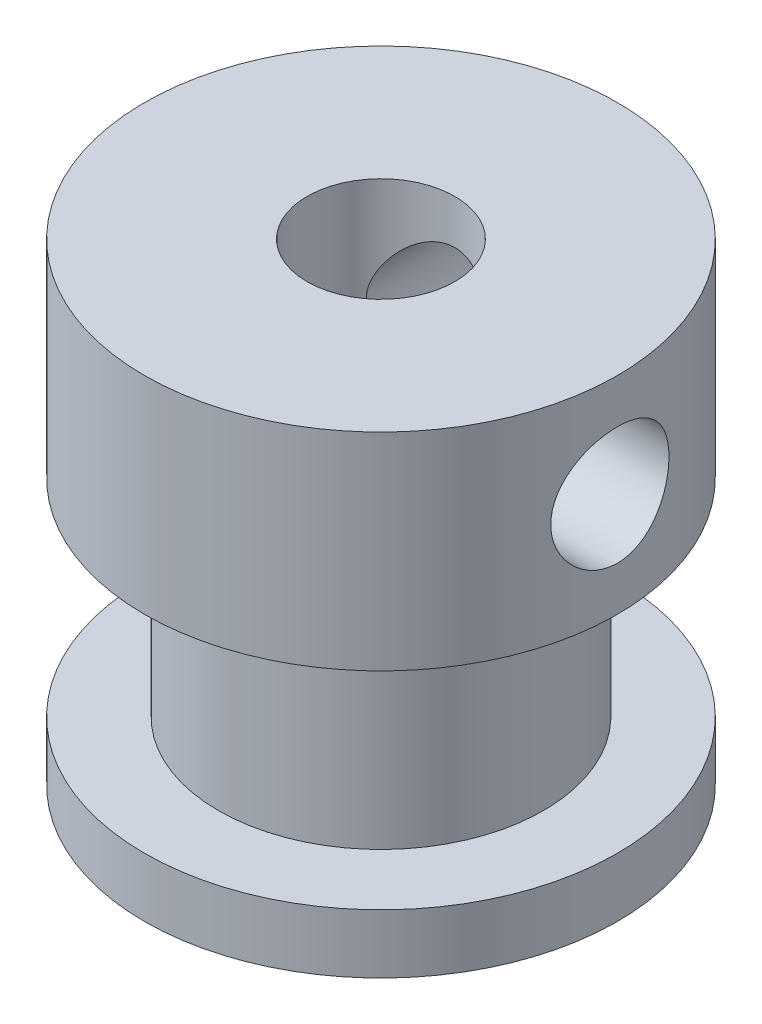
SolidWorks part; units mm, degrees
ref_plane "Front Plane" through (0, 0, 0) normal (0, 0, 1) x (1, 0, 0)
ref_plane "Top Plane" through (0, 0, 0) normal (0, 1, 0) x (1, 0, 0)
ref_plane "Right Plane" through (0, 0, 0) normal (1, 0, 0) x (0, 0, -1)
sketch "Sketch1" plane through (0, 0, 0) normal (0, 1, 0) x (1, 0, 0)
  circle A0 centre (0, 0) radius 8
  dimension "D1" = 16
extrude "Boss-Extrude1" add sketch "Sketch1" along normal blind 2
sketch "Sketch2" plane through (0, 2, 0) normal (0, 1, 0) x (1, 0, 0)
  circle A0 centre (0, 0) radius 5.5
  dimension "D1" = 11
extrude "Boss-Extrude2" add sketch "Sketch2" along normal blind 7
sketch "Sketch3" plane through (0, 9, 0) normal (0, 1, 0) x (1, 0, 0)
  circle A0 centre (0, 0) radius 8
  dimension "D1" = 16
extrude "Boss-Extrude3" add sketch "Sketch3" along normal blind 7
sketch "Sketch4" plane through (0, 16, 0) normal (0, 1, 0) x (1, 0, 0)
  circle A0 centre (0, 0) radius 2.5
  dimension "D1" = 5
extrude "Cut-Extrude2" cut sketch "Sketch4" against normal through all
sketch "Sketch7" plane through (0, 0, 0) normal (0, 0, 1) x (1, 0, 0)
  line L0 (8, 16) -> (-8, 16) construction
  circle A0 centre (0, 12.5) radius 2
  dimension "D2" = 4
  dimension "D1" = 3.5
extrude "Cut-Extrude3" cut sketch "Sketch7" against normal through all
pattern_circular "CirPattern1" count 2 every 90 about axis through (0, 16, 0) along (0, -1, 0) of "Cut-Extrude3"
